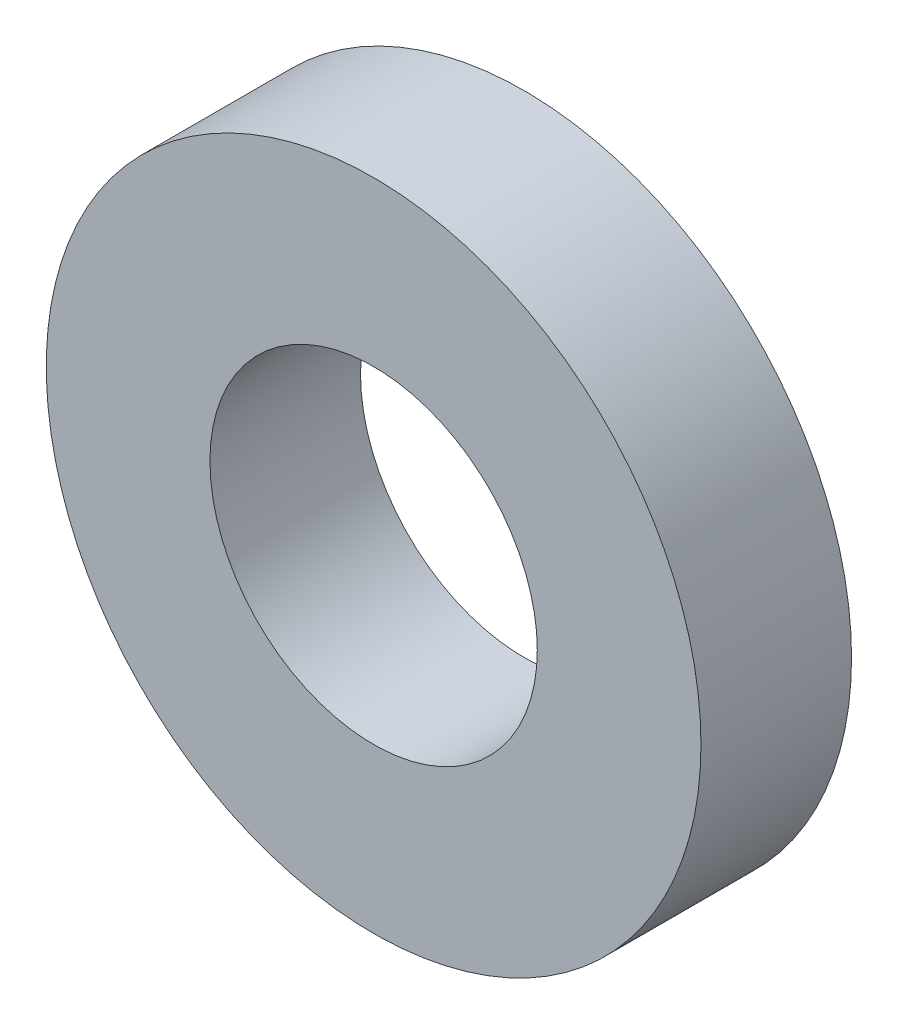
SolidWorks part; units mm, degrees
ref_plane "Front Plane" through (0, 0, 0) normal (0, 0, 1) x (1, 0, 0)
ref_plane "Top Plane" through (0, 0, 0) normal (0, 1, 0) x (1, 0, 0)
ref_plane "Right Plane" through (0, 0, 0) normal (1, 0, 0) x (0, 0, -1)
sketch "Sketch1" plane through (0, 0, 0) normal (0, 0, 1) x (1, 0, 0)
  circle A0 centre (0, 0) radius 1.5
  circle A1 centre (0, 0) radius 3
  dimension "D1" = 3
  dimension "D2" = 6
extrude "Boss-Extrude1" add sketch "Sketch1" along normal blind 1.38
